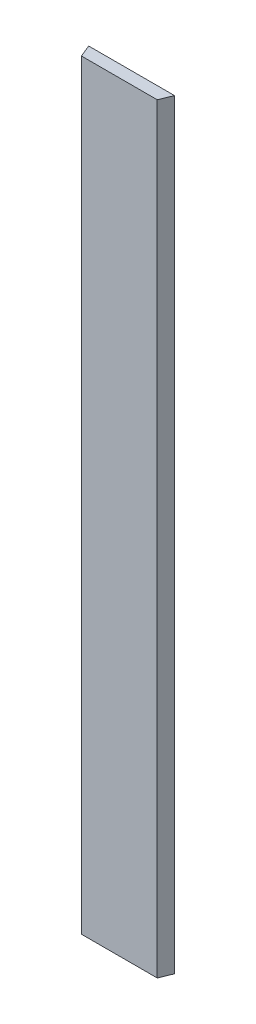
SolidWorks part; units mm, degrees
ref_plane "Plan de face" through (0, 0, 0) normal (0, 0, 1) x (1, 0, 0)
ref_plane "Plan de dessus" through (0, 0, 0) normal (0, 1, 0) x (1, 0, 0)
ref_plane "Plan de droite" through (0, 0, 0) normal (1, 0, 0) x (0, 0, -1)
sketch "Esquisse1" plane through (0, 0, 0) normal (0, 1, 0) x (1, 0, 0)
  line L0 (0, 0) -> (30.89, 0)
  line L1 (-2.055, 5) -> (32.945, 5)
  line L2 (32.945, 5) -> (30.89, 0)
  line L3 (-2.055, 5) -> (0, 0)
  point P5 (15.445, 0)
  point P6 (15.445, 5)
  dimension "D1" = 30.89
  dimension "D2" = 5
  dimension "D3" = 35
extrude "Boss.-Extru.1" add sketch "Esquisse1" along normal blind 310
